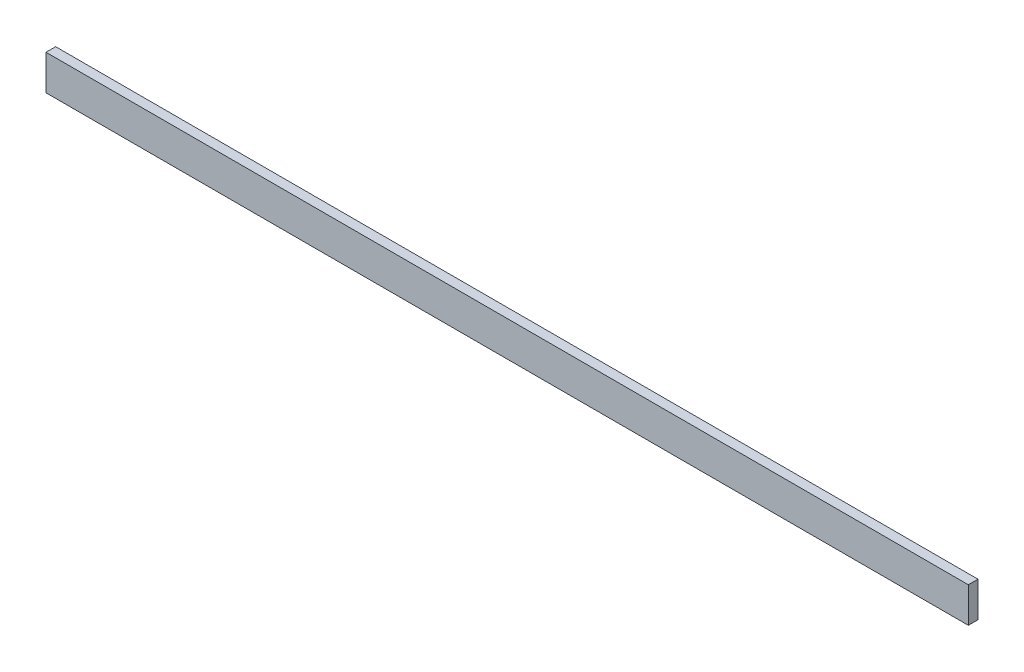
SolidWorks part; units mm, degrees
ref_plane "Face" through (0, 0, 0) normal (0, 0, 1) x (1, 0, 0)
ref_plane "Dessus" through (0, 0, 0) normal (0, 1, 0) x (1, 0, 0)
ref_plane "Droite" through (0, 0, 0) normal (1, 0, 0) x (0, 0, -1)
sketch "Esquisse1" plane through (0, 0, 0) normal (0, 1, 0) x (1, 0, 0)
  line L1 (0, 0) -> (2100, 0)
  line L2 (0, 0) -> (0, 22)
  line L3 (0, 22) -> (2100, 22)
  line L4 (2100, 0) -> (2100, 22)
  dimension "D1" = 2100
  dimension "D2" = 22
extrude "Extrusion1" add sketch "Esquisse1" along normal blind 80
